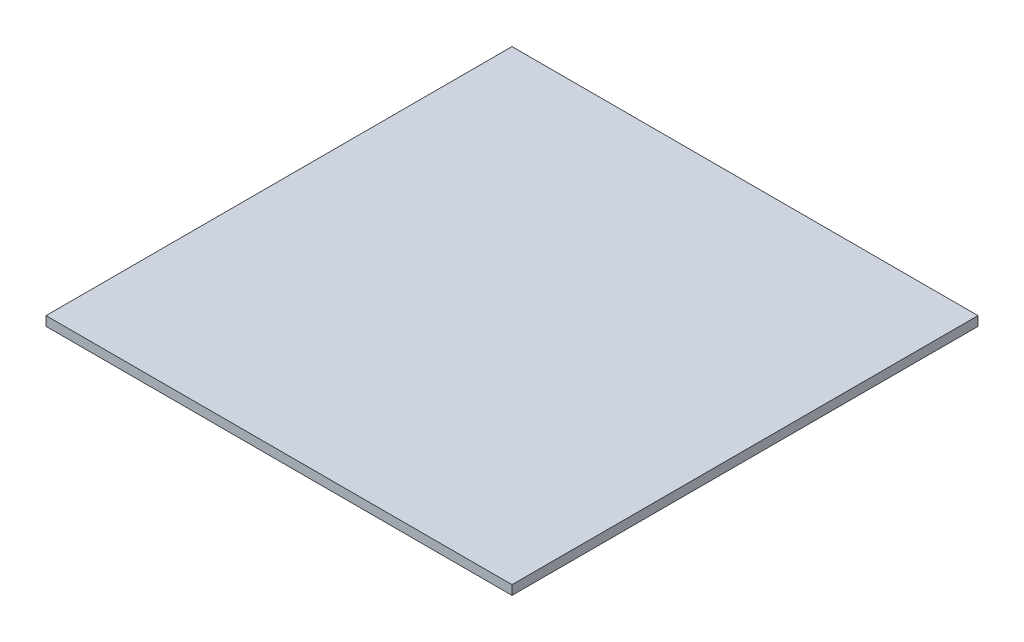
SolidWorks part; units mm, degrees
ref_plane "Front Plane" through (0, 0, 0) normal (0, 0, 1) x (1, 0, 0)
ref_plane "Top Plane" through (0, 0, 0) normal (0, 1, 0) x (1, 0, 0)
ref_plane "Right Plane" through (0, 0, 0) normal (1, 0, 0) x (0, 0, -1)
sketch "Sketch1" plane through (0, 0, 0) normal (0, 1, 0) x (1, 0, 0)
  line L1 (0, 0) -> (1270, 0)
  line L2 (0, 0) -> (0, 1270)
  line L3 (0, 1270) -> (1270, 1270)
  line L4 (1270, 0) -> (1270, 1270)
  dimension "D1" = 1270
  dimension "D2" = 1270
extrude "Boss-Extrude1" add sketch "Sketch1" against normal blind 25.4
